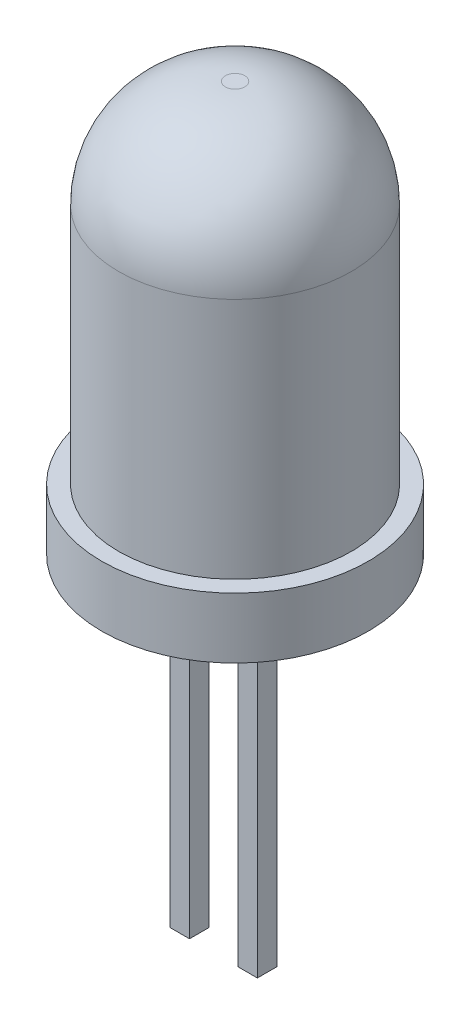
SolidWorks part; units mm, degrees
ref_plane "Front Plane" through (0, 0, 0) normal (0, 0, 1) x (1, 0, 0)
ref_plane "Top Plane" through (0, 0, 0) normal (0, 1, 0) x (1, 0, 0)
ref_plane "Right Plane" through (0, 0, 0) normal (1, 0, 0) x (0, 0, -1)
sketch "Sketch1" plane through (0, 0, 0) normal (0, 1, 0) x (1, 0, 0)
  circle A0 centre (0, 0) radius 2.75
  dimension "D1" = 5.5
extrude "Boss-Extrude1" add sketch "Sketch1" along normal blind 1.25
sketch "Sketch2" plane through (0, 1.25, 0) normal (0, 1, 0) x (1, 0, 0)
  circle A0 centre (0, 0) radius 2.4
  dimension "D1" = 4.8
extrude "Boss-Extrude2" add sketch "Sketch2" along normal blind 7.2
fillet "Fillet1" radius 2.2 1 edges at (0, 8.45, 2.4)
sketch "Sketch3" plane through (0, 0, 0) normal (0, -1, 0) x (1, 0, 0)
  line L1 (-1.2, 0.1397) -> (-0.8, 0.1397)
  line L2 (-1.2, 0.1397) -> (-1.2, -0.2603)
  line L3 (-1.2, -0.2603) -> (-0.8, -0.2603)
  line L4 (-0.8, 0.1397) -> (-0.8, -0.2603)
  line L5 (-1.2, 0.1397) -> (-0.8, -0.2603) construction
  line L6 (-1.2, -0.2603) -> (-0.8, 0.1397) construction
  point P0 (-1, -0.0603)
  dimension "D1" = 0.4
  dimension "D2" = 0.4
  dimension "D3" = 1
extrude "Boss-Extrude3" add sketch "Sketch3" along normal blind 7.2
ref_plane "Plane1" through (-0.3, 0, 0) normal (1, 0, 0) x (0, 0, -1)
mirror "Mirror2" about plane through (-0.3, 0, 0) normal (1, 0, 0) of "Boss-Extrude3"
